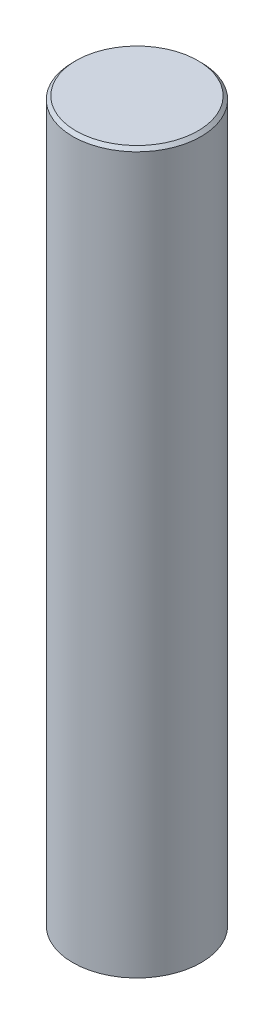
SolidWorks part; units mm, degrees
ref_plane "Front Plane" through (0, 0, 0) normal (0, 0, 1) x (1, 0, 0)
ref_plane "Top Plane" through (0, 0, 0) normal (0, 1, 0) x (1, 0, 0)
ref_plane "Right Plane" through (0, 0, 0) normal (1, 0, 0) x (0, 0, -1)
sketch "Sketch1" plane through (0, 0, 0) normal (0, 1, 0) x (1, 0, 0)
  circle A0 centre (0, 0) radius 20
  dimension "D1" = 40
extrude "Boss-Extrude1" add sketch "Sketch1" along normal blind 224
chamfer "Chamfer2" distance 1 angle 45 1 edges at (0, 224, 20)
